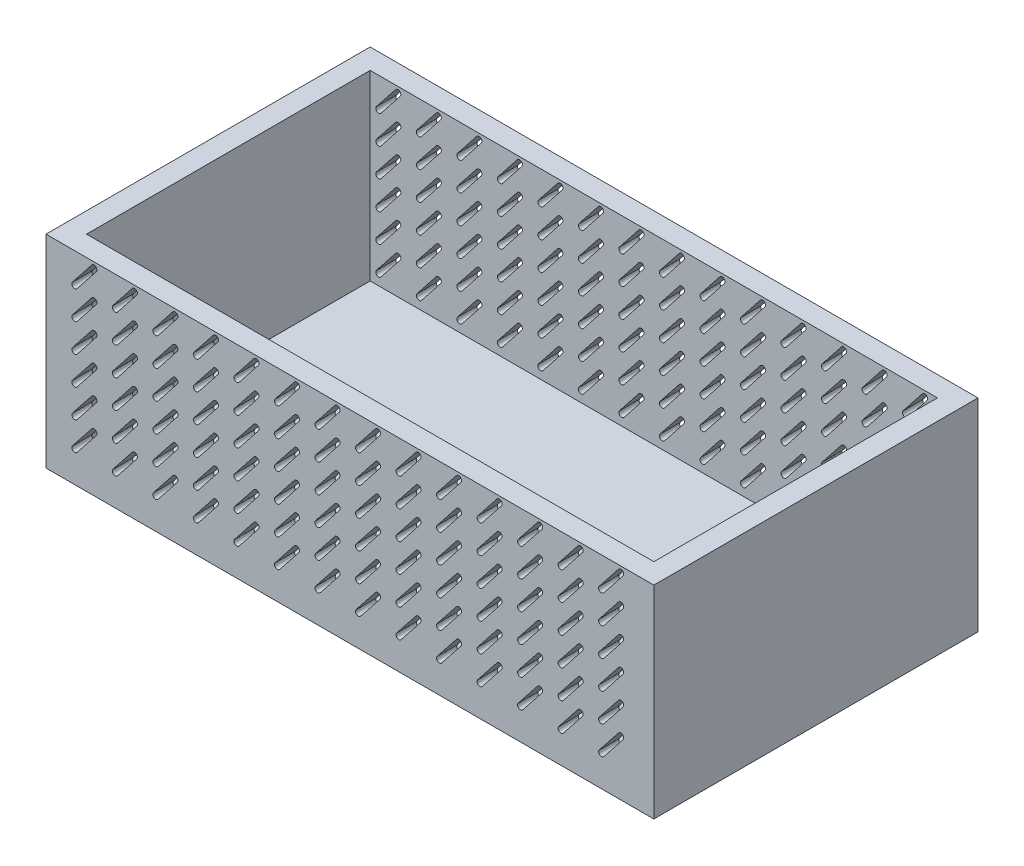
SolidWorks part; units mm, degrees
ref_plane "Plan de face" through (0, 0, 0) normal (0, 0, 1) x (1, 0, 0)
ref_plane "Plan de dessus" through (0, 0, 0) normal (0, 1, 0) x (1, 0, 0)
ref_plane "Plan de droite" through (0, 0, 0) normal (1, 0, 0) x (0, 0, -1)
sketch "Esquisse2" plane through (0, 0, 0) normal (0, 1, 0) x (1, 0, 0)
  line L1 (150, -80) -> (-150, -80)
  line L2 (150, -80) -> (150, 80)
  line L3 (150, 80) -> (-150, 80)
  line L4 (-150, -80) -> (-150, 80)
  line L5 (150, -80) -> (-150, 80) construction
  line L6 (150, 80) -> (-150, -80) construction
  point P0 (0, 0)
  dimension "D1" = 300
  dimension "D2" = 160
extrude "Boss.-Extru.1" add sketch "Esquisse2" against normal blind 100 contours L1 L4 L3 L2
shell "Coque2" thickness 10
sketch "Esquisse4" plane through (0, 0, -70) normal (0, 0, 1) x (1, 0, 0)
  line L1 (140, 0) -> (-140, 0)
  line L2 (140, 0) -> (140, -90)
  line L3 (140, -90) -> (-140, -90)
  line L4 (-140, 0) -> (-140, -90)
  line L5 (140, 0) -> (-140, -90) construction
  line L6 (140, -90) -> (-140, 0) construction
  point P0 (0, -45)
  dimension "D1" = 90
  dimension "D2" = 280
sketch "Esquisse5" plane through (0, 0, -70) normal (0, 0, 1) x (1, 0, 0)
  line L0 (-135.831, -14.8199) -> (-126.2975, -2.7858) construction
  line L1 (-136.9434, -13.9387) -> (-127.4099, -1.9046)
  line L2 (-134.7187, -15.7011) -> (-125.1852, -3.6671)
  arc A0 (-136.9434, -13.9387) -> (-134.7187, -15.7011) centre (-135.831, -14.8199) ccw
  arc A1 (-125.1852, -3.6671) -> (-127.4099, -1.9046) centre (-126.2975, -2.7858) ccw
  point P2 (-131.0643, -8.8029)
extrude "Enlèv. mat.-Extru.1" cut sketch "Esquisse5" along normal mid plane 340
pattern_linear "Répétition linéaire3" count 6 spacing 14 along (0, -1, 0) count 14 spacing 20 along (1, 0, 0) of "Enlèv. mat.-Extru.1"
